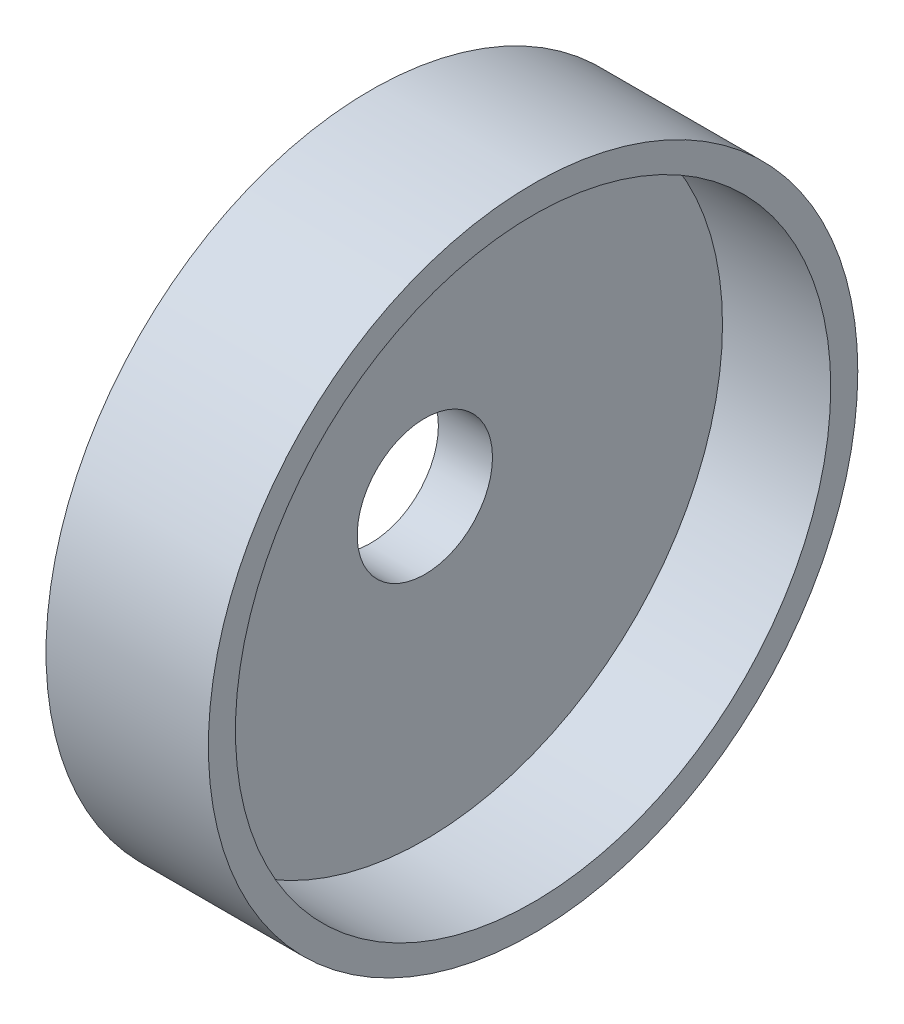
SolidWorks part; units mm, degrees
ref_plane "Front Plane" through (0, 0, 0) normal (0, 0, 1) x (1, 0, 0)
ref_plane "Top Plane" through (0, 0, 0) normal (0, 1, 0) x (1, 0, 0)
ref_plane "Right Plane" through (0, 0, 0) normal (1, 0, 0) x (0, 0, -1)
sketch "Sketch1" plane through (0, 0, 0) normal (1, 0, 0) x (0, 0, -1)
  circle A0 centre (0, 0) radius 60
  dimension "D1" = 120
extrude "Boss-Extrude1" add sketch "Sketch1" along normal blind 10
sketch "Sketch2" plane through (10, 0, 0) normal (1, 0, 0) x (0, 0, -1)
  circle A0 centre (0, 0) radius 60 construction
  circle A1 centre (0, 0) radius 60
  circle A2 centre (0, 0) radius 55
  dimension "D1" = 110
extrude "Boss-Extrude2" add sketch "Sketch2" along normal blind 20
sketch "Sketch3" plane through (10, 0, 0) normal (1, 0, 0) x (0, 0, -1)
  circle A0 centre (0, 0) radius 12.5
  dimension "D1" = 25
extrude "Cut-Extrude1" cut sketch "Sketch3" against normal through all
